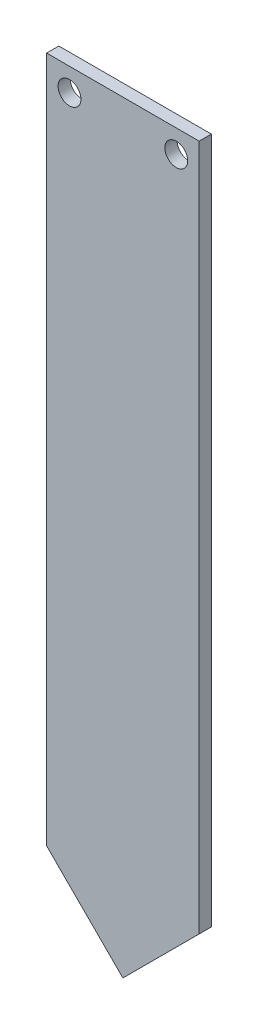
SolidWorks part; units mm, degrees
ref_plane "Ön Düzlem" through (0, 0, 0) normal (0, 0, 1) x (1, 0, 0)
ref_plane "Üst Düzlem" through (0, 0, 0) normal (0, 1, 0) x (1, 0, 0)
ref_plane "Sağ Düzlem" through (0, 0, 0) normal (1, 0, 0) x (0, 0, -1)
sketch "Çizim1" plane through (0, 0, 0) normal (0, 0, 1) x (1, 0, 0)
  line L0 (0, -55) -> (-10, -45)
  line L1 (-10, 45) -> (10, 45)
  line L2 (-10, 45) -> (-10, -45)
  line L4 (10, 45) -> (10, -45)
  line L5 (0, -55) -> (10, -45)
  circle A0 centre (-7, 42) radius 1.5
  circle A1 centre (7, 42) radius 1.5
  point P4 (0, 45)
  point P6 (-10, 0)
  point P14 (0, 0)
  point P15 (0, 0)
  dimension "D3" = 3
  dimension "D4" = 3
  dimension "D1" = 90
  dimension "D2" = 20
  dimension "D5" = 3
  dimension "D6" = 3
  dimension "D7" = 3
  dimension "D8" = 10
  dimension "D9" = 90
extrude "Yükseklik-Ekstrüzyon1" add sketch "Çizim1" along normal blind 1.6
